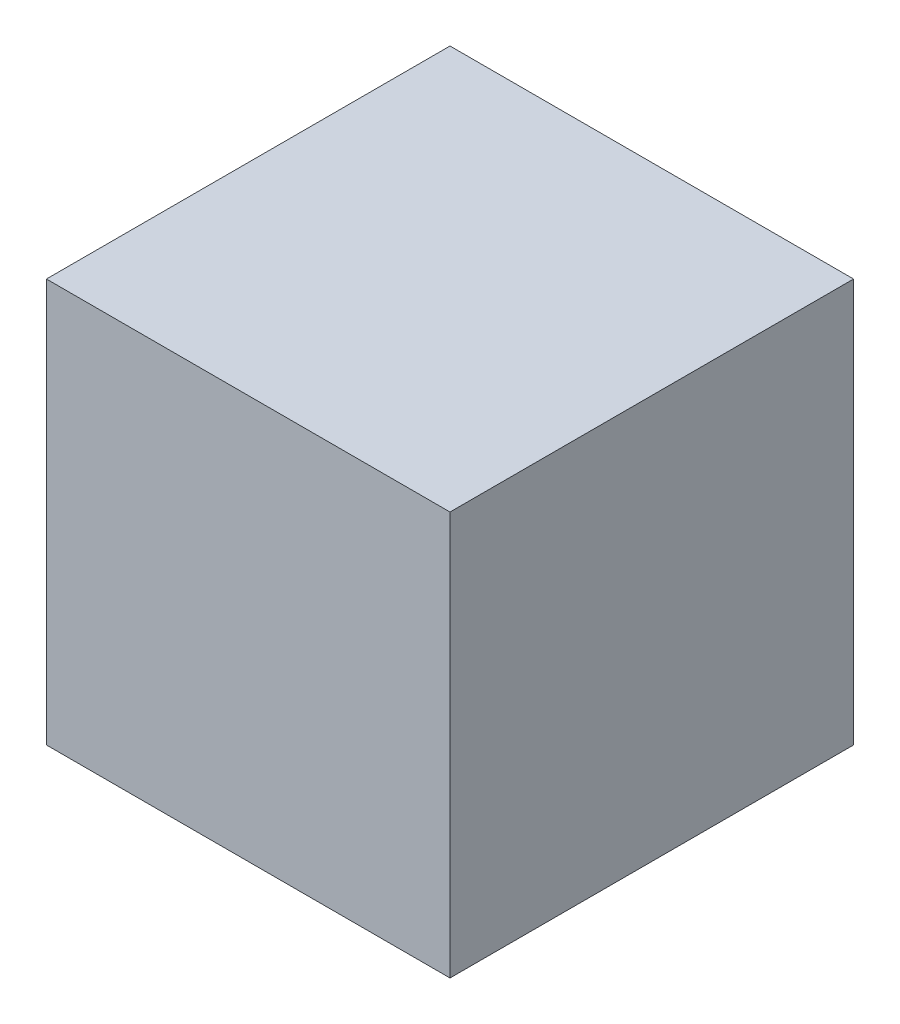
SolidWorks part; units mm, degrees
material "玻璃"
ref_plane "前视基准面" through (0, 0, 0) normal (0, 0, 1) x (1, 0, 0)
ref_plane "上视基准面" through (0, 0, 0) normal (0, 1, 0) x (1, 0, 0)
ref_plane "右视基准面" through (0, 0, 0) normal (1, 0, 0) x (0, 0, -1)
other "Configuration Table"
sketch "草图1" plane through (0, 0, 0) normal (0, 0, 1) x (1, 0, 0)
  line L1 (-300, -300) -> (300, -300)
  line L2 (-300, -300) -> (-300, 300)
  line L3 (-300, 300) -> (300, 300)
  line L4 (300, -300) -> (300, 300)
  line L5 (-300, -300) -> (300, 300) construction
  line L6 (-300, 300) -> (300, -300) construction
  point P0 (0, 0)
  dimension "D1" = 600
extrude "凸台-拉伸1" add sketch "草图1" along normal blind 600
